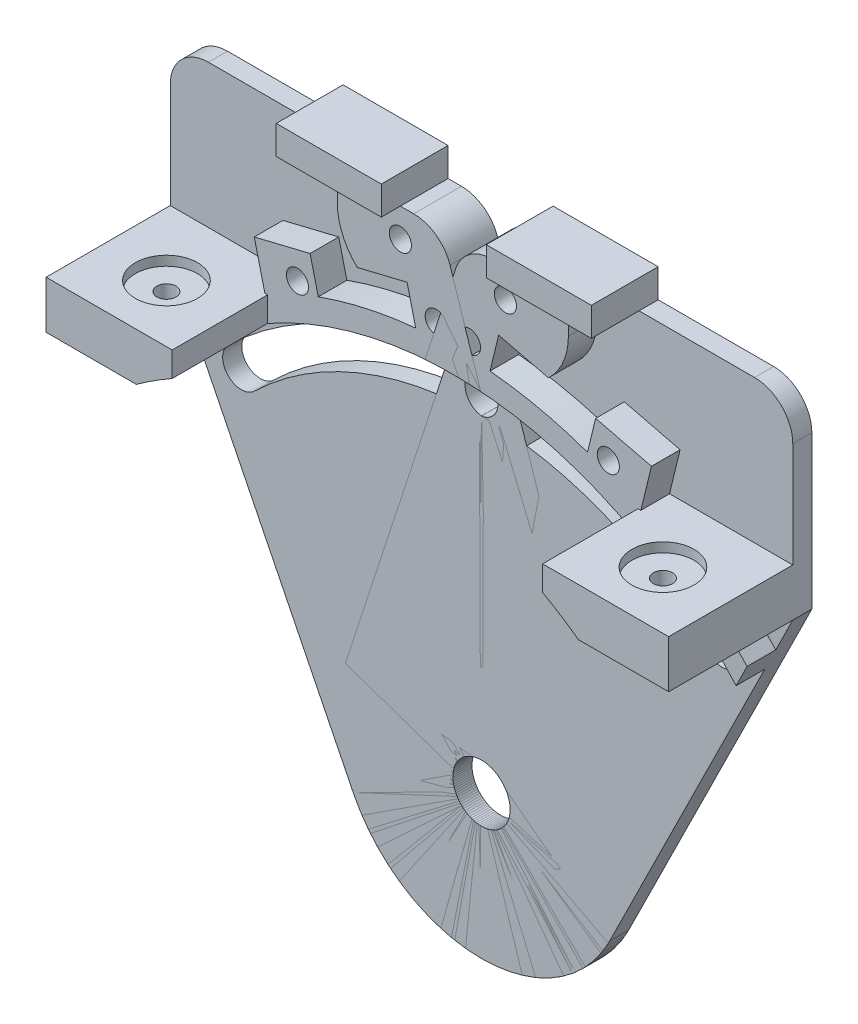
SolidWorks part; units mm, degrees
ref_plane "Front Plane" through (0, 0, 0) normal (0, 0, 1) x (1, 0, 0)
ref_plane "Top Plane" through (0, 0, 0) normal (0, 1, 0) x (1, 0, 0)
ref_plane "Right Plane" through (0, 0, 0) normal (1, 0, 0) x (0, 0, -1)
sketch "Sketch1" plane through (0, 0, 0) normal (0, 0, 1) x (1, 0, 0)
  line L12 (-28.2, 23.755) -> (-28.2, -23.755)
  line L13 (-23.755, -28.2) -> (23.755, -28.2)
  line L14 (28.2, -23.755) -> (28.2, 23.755)
  line L15 (23.755, 28.2) -> (-23.755, 28.2)
  circle A0 centre (0, 0) radius 19.05
  circle A1 centre (-23.57, 23.57) radius 2.55
  circle A2 centre (23.57, 23.57) radius 2.55
  circle A3 centre (23.57, -23.57) radius 2.55
  circle A4 centre (-23.57, -23.57) radius 2.55
  arc A12 (-23.755, 28.2) -> (-28.2, 23.755) centre (-23.755, 23.755) ccw
  arc A13 (-28.2, -23.755) -> (-23.755, -28.2) centre (-23.755, -23.755) ccw
  arc A14 (23.755, -28.2) -> (28.2, -23.755) centre (23.755, -23.755) ccw
  arc A15 (28.2, 23.755) -> (23.755, 28.2) centre (23.755, 23.755) ccw
sketch "Sketch2" plane through (0, 0, 0) normal (0, 0, 1) x (1, 0, 0)
  line L0 (-33.02, 0) -> (-33.02, 66.04) construction
  line L1 (-17.0688, -8.4592) -> (-41.402, 40.64)
  line L2 (-41.402, 66.04) -> (-1.524, 66.04)
  line L3 (-1.524, 66.04) -> (18.1091, 5.9131)
  line L4 (-41.402, 40.64) -> (-41.402, 66.04)
  arc A0 (-17.0688, -8.4592) -> (18.1091, 5.9131) centre (0, 0) ccw
  circle A1 centre (0, 0) radius 33.02 construction
  circle A2 centre (0, 0) radius 38.1 construction
  circle A3 centre (0, 0) radius 3.81
  dimension "D1" = 38.1
  dimension "D2" = 66.04
  dimension "D3" = 66.04
  dimension "D5" = 76.2
  dimension "D8" = 7.62
  dimension "D4" = 39.878
  dimension "D6" = 8.382
  dimension "D7" = 25.4
extrude "Boss-Extrude1" add sketch "Sketch2" along normal blind 2.54
sketch "Sketch5" plane through (0, 0, 2.54) normal (0, 0, 1) x (1, 0, 0)
  line L0 (-33.02, 0) -> (-33.02, 66.04) construction
  line L1 (-24.638, 40.64) -> (-41.402, 40.64)
  line L2 (-24.638, 40.64) -> (-24.638, 46.99)
  line L3 (-24.638, 46.99) -> (-41.402, 46.99)
  line L4 (-41.402, 40.64) -> (-41.402, 46.99)
  line L5 (-24.638, 40.64) -> (-41.402, 46.99) construction
  line L6 (-24.638, 46.99) -> (-41.402, 40.64) construction
  point P0 (-33.02, 43.815)
  dimension "D1" = 6.35
extrude "Boss-Extrude2" add sketch "Sketch5" along normal blind 16.51
sketch "Sketch6" plane through (0, 46.99, 0) normal (0, 1, 0) x (1, 0, 0)
  line L0 (-33.02, -2.54) -> (-33.02, -19.05) construction
  line L1 (-24.638, -2.54) -> (-41.402, -2.54) construction
  line L2 (-24.638, -19.05) -> (-41.402, -19.05) construction
  line L3 (-1.524, -2.54) -> (-41.402, -2.54) construction
  circle A0 centre (-33.02, -11.43) radius 4.1275
  dimension "D1" = 8.255
  dimension "0.4" = 8.89
extrude "Cut-Extrude2" cut sketch "Sketch6" against normal blind 1.27
sketch "Sketch7" plane through (0, 45.72, 0) normal (0, 1, 0) x (1, 0, 0)
  circle A0 centre (-33.02, -11.43) radius 1.27
  dimension "D1" = 2.54
extrude "Cut-Extrude3" cut sketch "Sketch7" against normal through all
sketch "Sketch9" plane through (0, 0, 0) normal (0, 0, -1) x (-1, 0, 0)
  line L0 (6.9839, 62.23) -> (3.1711, 62.23) construction
  line L1 (3.1711, 62.23) -> (5.0775, 58.928)
  line L2 (5.0775, 58.928) -> (8.8904, 58.928)
  line L3 (8.8904, 58.928) -> (10.7968, 62.23)
  line L4 (10.7968, 62.23) -> (8.8904, 65.532)
  line L5 (8.8904, 65.532) -> (5.0775, 65.532)
  line L6 (5.0775, 65.532) -> (3.1711, 62.23)
  line L7 (6.9839, 60.5028) -> (6.9839, 63.9572) construction
  line L8 (24.3799, 49.664) -> (23.3081, 53.3231)
  line L9 (23.3081, 53.3231) -> (19.6034, 54.2245)
  line L10 (19.6034, 54.2245) -> (16.9704, 51.4668)
  line L11 (16.9704, 51.4668) -> (18.0421, 47.8077)
  line L12 (18.0421, 47.8077) -> (21.7469, 46.9063)
  line L13 (21.7469, 46.9063) -> (24.3799, 49.664)
  line L14 (5.9185, 54.1558) -> (4.8467, 57.8149)
  line L15 (4.8467, 57.8149) -> (1.142, 58.7163)
  line L16 (1.142, 58.7163) -> (-1.491, 55.9586)
  line L17 (-1.491, 55.9586) -> (-0.4193, 52.2995)
  line L18 (-0.4193, 52.2995) -> (3.2855, 51.3981)
  line L19 (3.2855, 51.3981) -> (5.9185, 54.1558)
  line L21 (24.9034, 50.8527) -> (-13.9627, 60.3092) construction
  circle A0 centre (6.9839, 62.23) radius 3.302 construction
  circle A1 centre (20.6751, 50.5654) radius 3.302 construction
  circle A2 centre (2.2137, 55.0572) radius 3.302 construction
  circle A3 centre (6.9839, 62.23) radius 1.7272 construction
  circle A4 centre (2.2137, 55.0572) radius 1.5 construction
  circle A5 centre (20.6751, 50.5654) radius 1.5 construction
  dimension "D1" = 6.604
  dimension "D2" = 6.604
  dimension "D3" = 6.604
extrude "Cut-Extrude4" cut sketch "Sketch9" against normal blind 2.286
sketch "Sketch8" plane through (0, 0, 2.54) normal (0, 0, 1) x (1, 0, 0)
  line L0 (-41.402, 66.04) -> (-1.524, 66.04) construction
  line L1 (-15.367, 66.04) -> (-6.9839, 66.04)
  line L2 (-15.367, 66.04) -> (-15.367, 62.23)
  line L3 (-14.4512, 58.42) -> (-6.9839, 58.42) construction
  line L4 (-6.9839, 66.04) -> (-6.9839, 58.42) construction
  line L5 (-15.875, 63.5) -> (-15.875, 55.88) construction
  line L6 (-18.9903, 54.5774) -> (0.6579, 59.358) construction
  line L8 (-15.367, 62.23) -> (-6.9839, 62.23) construction
  line L9 (-6.9839, 66.04) -> (-1.524, 66.04)
  line L10 (-1.524, 66.04) -> (3.0918, 51.9041)
  line L11 (18.1091, 5.9131) -> (-1.524, 66.04) construction
  line L12 (-5.8104, 55.4982) -> (-4.2737, 49.1825) construction
  line L13 (-1.524, 66.04) -> (18.1091, 5.9131) construction
  line L14 (-4.2737, 49.1825) -> (-16.6817, 46.1635) construction
  line L15 (-16.6817, 46.1635) -> (-18.7435, 54.6374) construction
  line L16 (-6.0887, 57.7165) -> (-4.2404, 50.1201)
  line L17 (-17.142, 46.981) -> (-18.9903, 54.5774)
  line L18 (3.0918, 51.9041) -> (-4.2404, 50.1201)
  line L19 (-24.9034, 53.1387) -> (13.9627, 62.5952) construction
  line L20 (-5.5636, 55.5583) -> (-4.0269, 49.2425) construction
  line L21 (-12.7085, 56.1058) -> (-6.0887, 57.7165)
  line L22 (-16.9285, 46.1034) -> (-18.9903, 54.5774) construction
  line L23 (-17.142, 46.981) -> (-24.5674, 45.1744)
  line L24 (-24.5674, 45.1744) -> (-26.4157, 52.7707)
  line L25 (-26.4157, 52.7707) -> (-18.9903, 54.5774)
  line L26 (-21.1208, 35.3063) -> (-24.9034, 50.8527) construction
  line L27 (0.4193, 52.2995) -> (-3.2855, 51.3981) construction
  arc A0 (-6.9839, 58.42) -> (-6.9839, 66.04) centre (-6.9839, 62.23) ccw construction
  circle A1 centre (-20.6751, 50.5654) radius 3.4925 construction
  circle A2 centre (-2.2137, 55.0572) radius 3.4925 construction
  arc A3 (-15.367, 62.23) -> (-12.7085, 56.1058) centre (-6.9839, 62.23) ccw
  point P29 (-6.9839, 62.23)
  point P50 (-20.6751, 50.5654)
  point P52 (-2.2137, 55.0572)
  dimension "D2" = 6.985
  dimension "D3" = 6.985
  dimension "D1" = 0.508
  dimension "D4" = 0.254
  dimension "D5" = 1.016
  dimension "D6" = 1.016
extrude "Boss-Extrude3" add sketch "Sketch8" along normal blind 3.81
hole_wizard "#4 Clearance Hole1" positions "Sketch11" profile "Sketch10" hole size "#4" standard "ANSI Inch" end condition through all
sketch "Sketch11" plane through (0, 0, 6.35) normal (0, 0, 1) x (1, 0, 0)
  point P0 (-6.9839, 62.23)
  point P4 (-20.6751, 50.5654)
  point P7 (-2.2137, 55.0572)
sketch "Sketch10" plane through (-6.9839, 62.23, 6.35) normal (1, 0, 0) x (0, -1, 0)
  line L0 (0, 0) -> (0, 6.35)
  line L1 (0, 6.35) -> (1.4732, 6.35)
  line L2 (1.4732, 6.35) -> (1.4732, 0)
  line L5 (1.4732, 0) -> (0, 0)
  line L11 (0, -6.35) -> (0, 107.95) construction
  dimension "Thru Hole Dia." = 2.9464
  dimension "Thru Hole Depth" = 6.35
sketch "Sketch14" plane through (0, 0, 2.54) normal (0, 0, 1) x (1, 0, 0)
  line L1 (-41.402, 66.04) -> (-1.524, 66.04) construction
  line L2 (-6.9839, 60.7568) -> (-6.9839, 66.04) construction
  line L3 (-6.9839, 66.04) -> (-20.9539, 66.04)
  line L6 (-6.9839, 66.04) -> (-6.9839, 69.85)
  line L8 (-6.9839, 69.85) -> (-20.9539, 69.85)
  line L9 (-20.9539, 66.04) -> (-20.9539, 69.85)
  circle A0 centre (-6.9839, 62.23) radius 1.4732 construction
  point P0 (-6.9839, 62.23)
  dimension "D1" = 3.81
  dimension "D2" = 13.97
extrude "Boss-Extrude6" add sketch "Sketch14" along normal blind 6.35 and the other way through all
fillet "Fillet1" radius 5.08 2 edges at (-1.524, 66.04, 3.175) (-41.402, 66.04, 1.27)
sketch "Sketch15" plane through (0, 0, 2.54) normal (0, 0, 1) x (1, 0, 0)
  line L0 (-17.0688, -8.4592) -> (-41.402, 40.64) construction
  line L1 (-1.524, 66.04) -> (18.1091, 5.9131) construction
  arc A0 (-31.9429, 32.9938) -> (-0.299, 45.9222) centre (0, 0) cw construction
  circle A1 centre (0, 0) radius 3.81 construction
  arc A2 (-0.3152, 48.4114) -> (-33.6744, 34.7821) centre (0, 0) ccw
  arc A3 (-0.2828, 43.4331) -> (-30.2115, 31.2054) centre (0, 0) ccw
  arc A4 (-0.2828, 43.4331) -> (-0.3152, 48.4114) centre (-0.299, 45.9222) ccw
  arc A5 (-33.6744, 34.7821) -> (-30.2115, 31.2054) centre (-31.9429, 32.9938) ccw
  point P6 (-17.3687, 42.512)
  dimension "D1" = 4.9784
  dimension "D4" = 45.9232
  dimension "D2" = 5.08
  dimension "D3" = 5.08
extrude "Cut-Extrude5" cut sketch "Sketch15" against normal through all
sketch "Sketch18" plane through (0, 0, 2.54) normal (0, 0, 1) x (1, 0, 0)
  line L0 (-1.524, 66.04) -> (18.1091, 5.9131) construction
  line L1 (-17.0688, -8.4592) -> (-41.402, 40.64) construction
  line L2 (3.7043, 50.028) -> (2.6806, 53.1633)
  line L3 (-37.676, 33.1217) -> (-39.1405, 36.0768)
  arc A0 (-31.9429, 32.9938) -> (-0.299, 45.9222) centre (0, 0) cw
  arc A1 (-0.299, 45.9222) -> (-31.9429, 32.9938) centre (0, 0) ccw construction
  arc A2 (-37.676, 33.1217) -> (3.7043, 50.028) centre (0, 0) cw
  arc A3 (-29.0124, 35.598) -> (-5.9439, 45.5369) centre (0, 0) cw construction
  arc A4 (-31.6922, 38.8861) -> (-6.4929, 49.743) centre (0, 0) cw construction
  arc A5 (-39.1405, 36.0768) -> (2.6806, 53.1633) centre (0, 0) cw
  arc A6 (-39.9785, 35.1459) -> (3.9307, 53.0855) centre (0, 0) cw construction
  point P20 (-25.0092, 46.99)
  line M10 (-24.638, 45.4645) -> (-24.638, 41.6741)
  line M11 (-26.3088, 40.64) -> (-41.402, 40.64)
  line M12 (-41.402, 40.64) -> (-17.0688, -8.4592)
  line M14 (18.1091, 5.9131) -> (3.0918, 51.9041)
  line M15 (3.0918, 51.9041) -> (-4.2404, 50.1201)
  line M16 (-4.2404, 50.1201) -> (-6.0887, 57.7165)
  line M22 (-17.142, 46.981) -> (-24.5674, 45.1744)
  line M23 (-24.5674, 45.1744) -> (-24.638, 45.4645)
  line M25 (-18.9903, 54.5774) -> (-17.142, 46.981)
  dimension "D1" = 4.2418
extrude "Boss-Extrude7" add sketch "Sketch18" along normal blind 3.81 contours A5 A2 M12 M11 | A5 A2 M10 M14 M15 M16 M25 M22 M23 | A2 M10 M22 M23
sketch "Sketch16" plane through (0, 0, 2.54) normal (0, 0, 1) x (1, 0, 0)
  arc A0 (-31.9429, 32.9938) -> (-0.299, 45.9222) centre (0, 0) cw construction
  arc A1 (-0.3266, 50.1639) -> (-34.8934, 36.0413) centre (0, 0) ccw
  arc A2 (-0.2713, 41.6805) -> (-28.9925, 29.9462) centre (0, 0) ccw
  arc A3 (-0.2713, 41.6805) -> (-0.3266, 50.1639) centre (-0.299, 45.9222) ccw
  arc A4 (-34.8934, 36.0413) -> (-28.9925, 29.9462) centre (-31.9429, 32.9938) ccw
  point P3 (-17.3687, 42.512)
  dimension "D3" = 45.9232
  dimension "D1" = 8.4836
  dimension "D2" = 43.7
extrude "Cut-Extrude7" cut sketch "Sketch16" along normal through all
sketch "Sketch13" plane through (0, 0, 0) normal (0, 0, -1) x (-1, 0, 0)
  line L1 (41.402, 66.04) -> (1.524, 66.04) construction
  line L3 (1.524, 66.04) -> (-18.1091, 5.9131) construction
  circle A0 centre (-6.7754, 40.6227) radius 6.35
  circle A1 centre (21.463, 66.04) radius 6.35
  circle A2 centre (41.402, 40.64) radius 6.35
  circle A3 centre (16.3338, -9.8036) radius 6.35
  arc A4 (-18.1091, 5.9131) -> (17.0688, -8.4592) centre (0, 0) ccw construction
  circle A5 centre (-16.3338, -9.8036) radius 6.35
  circle A6 centre (-16.3338, 11.3499) radius 6.35
  arc A8 (0.3152, 48.4114) -> (0.2828, 43.4331) centre (0.299, 45.9222) ccw construction
  dimension "D1" = 12.7
  dimension "D2" = 12.7
  dimension "D3" = 12.7
  dimension "D4" = 12.7
  dimension "D5" = 12.7
  dimension "D6" = 12.7
extrude "Print Tabs" [suppressed] add sketch "Sketch13" against normal blind 0.4
mirror "Mirror1" about plane through (0, 0, 0) normal (1, 0, 0) of bodies 122 118
